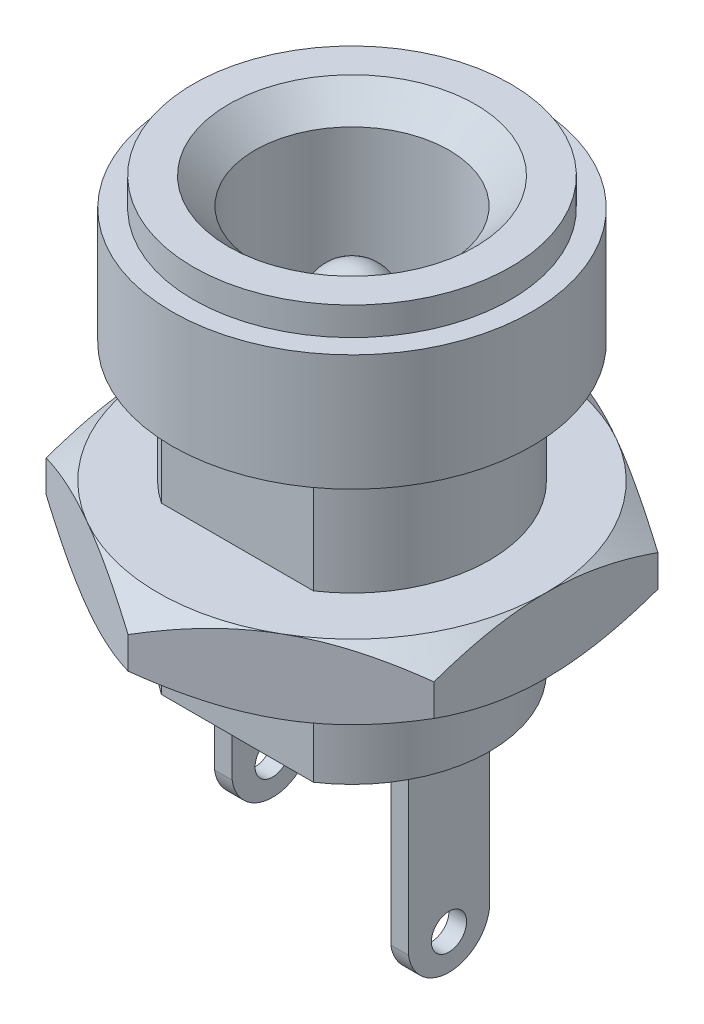
SolidWorks part; units mm, degrees
ref_plane "Front Plane" through (0, 0, 0) normal (0, 0, 1) x (1, 0, 0)
ref_plane "Top Plane" through (0, 0, 0) normal (0, 1, 0) x (1, 0, 0)
ref_plane "Right Plane" through (0, 0, 0) normal (1, 0, 0) x (0, 0, -1)
sketch "Sketch1" plane through (0, 0, 0) normal (0, 0, 1) x (1, 0, 0)
  line L0 (0, 0) -> (0, 12.2) construction
  line L1 (0, 0) -> (3.9, 0) construction
  line L2 (3.9, 0) -> (3.9, 8.1)
  line L3 (3.9, 8.1) -> (5.1, 8.1)
  line L4 (5.1, 8.1) -> (5.1, 11.4)
  line L5 (5.1, 11.4) -> (4.5, 11.4)
  line L6 (4.5, 11.4) -> (4.5, 12.2)
  line L7 (4.5, 12.2) -> (0, 12.2) construction
  line L8 (4.5, 12.2) -> (3.5, 12.2)
  line L9 (3.5, 12.2) -> (2.75, 11.45)
  line L10 (2.75, 11.45) -> (2.75, 3.2)
  line L11 (2.75, 3.2) -> (1.05, 3.2)
  line L12 (1.05, 3.2) -> (1.05, 8.95)
  line L13 (0, 2) -> (1.3, 2)
  line L14 (1.3, 2) -> (1.3, 0)
  line L15 (1.3, 0) -> (3.9, 0)
  line L16 (0, 10) -> (0, 2)
  arc A0 (1.05, 8.95) -> (0, 10) centre (0, 8.95) ccw
  dimension "D1" = 7.8
  dimension "D2" = 12.2
  dimension "D3" = 10.2
  dimension "D4" = 9
  dimension "D5" = 0.8
  dimension "D6" = 4.1
  dimension "D7" = 45
  dimension "D8" = 5.5
  dimension "D9" = 1
  dimension "D10" = 9
  dimension "D11" = 2.1
  dimension "D12" = 2.2
  dimension "D13" = 2.6
  dimension "D14" = 2
revolve "Revolve1" add sketch "Sketch1" angle 360 about L16
sketch "Sketch2" plane through (0, 0, 0) normal (0, -1, 0) x (1, 0, 0)
  line L0 (2.25, 0) -> (0, 0) construction
  line L1 (2.25, 1.15) -> (2.75, 1.15)
  line L2 (2.25, 1.15) -> (2.25, -1.15)
  line L3 (2.25, -1.15) -> (2.75, -1.15)
  line L4 (2.75, 1.15) -> (2.75, -1.15)
  line L5 (0, 0) -> (-2.25, 0) construction
  line L6 (-2.25, 1.15) -> (-2.75, 1.15)
  line L7 (-2.25, 1.15) -> (-2.25, -1.15)
  line L8 (-2.25, -1.15) -> (-2.75, -1.15)
  line L9 (-2.75, 1.15) -> (-2.75, -1.15)
  dimension "D1" = 2.75
  dimension "D2" = 2.3
  dimension "D3" = 0.5
extrude "Boss-Extrude1" add sketch "Sketch2" along normal blind 6
sketch "Sketch3" plane through (-2.75, 0, 0) normal (-1, 0, 0) x (0, 0, 1)
  line L0 (-1.15, -6) -> (-1.15, 0) construction
  line L1 (1.15, -6) -> (-1.15, -6)
  line L2 (1.15, -6) -> (1.15, -4.2)
  line L3 (1.15, -4.2) -> (-1.15, -4.2)
  line L4 (-1.15, -6) -> (-1.15, -4.2)
  dimension "D1" = 4.2
extrude "Cut-Extrude1" cut sketch "Sketch3" against normal up to next
sketch "Sketch4" plane through (-2.75, 0, 0) normal (-1, 0, 0) x (0, 0, 1)
  line L2 (1.15, -4.2) -> (-1.15, -4.2) construction
  line L3 (1.15, -4.2) -> (1.15, 0) construction
  line L4 (-1.15, -4.2) -> (-1.15, 0) construction
  line L5 (-1.15, -6) -> (-1.15, 0) construction
  line L6 (1.15, -6) -> (1.15, 0) construction
  line L7 (1.15, -6) -> (-1.15, -6) construction
  line L8 (-1.15, -3.2) -> (-1.15, -4.4)
  line L9 (-1.15, -4.4) -> (1.15, -4.4)
  line L10 (1.15, -4.4) -> (1.15, -3.2)
  circle A0 centre (0, -3.2) radius 0.5
  arc A1 (-1.15, -3.2) -> (1.15, -3.2) centre (0, -3.0388) ccw
  circle A2 centre (0, -5) radius 0.5 construction
  arc A3 (-1.15, -5) -> (1.15, -5) centre (0, -4.8387) ccw construction
  dimension "D1" = 1
  dimension "D2" = 3.2
  dimension "D3" = 5
  dimension "D4" = 1.2
extrude "Cut-Extrude2" cut sketch "Sketch4" against normal up to next
sketch "Sketch5" plane through (2.25, 0, 0) normal (-1, 0, 0) x (0, 0, 1)
  line L0 (-1.15, -5) -> (-1.15, -6.5)
  line L1 (-1.15, -6.5) -> (1.15, -6.5)
  line L2 (1.15, -6.5) -> (1.15, -5)
  circle A0 centre (0, -5) radius 0.5 construction
  arc A1 (-1.15, -5) -> (1.15, -5) centre (0, -4.8387) ccw construction
  circle A2 centre (0, -5) radius 0.5
  arc A3 (-1.15, -5) -> (1.15, -5) centre (0, -4.8387) ccw
  dimension "D1" = 1.5
extrude "Cut-Extrude3" cut sketch "Sketch5" against normal up to next
sketch "Sketch6" plane through (0, 0, 0) normal (0, -1, 0) x (1, 0, 0)
  line L0 (0, 3.25) -> (0, -3.25) construction
  line L1 (-5, 3.25) -> (5, 3.25)
  line L2 (-5, 3.25) -> (-5, 13.25)
  line L3 (-5, 13.25) -> (5, 13.25)
  line L4 (5, 3.25) -> (5, 13.25)
  line L5 (5, -3.25) -> (-5, -3.25)
  line L6 (5, -3.25) -> (5, -13.25)
  line L7 (5, -13.25) -> (-5, -13.25)
  line L8 (-5, -3.25) -> (-5, -13.25)
  point P10 (0, 0)
  dimension "D1" = 6.5
  dimension "D2" = 10
extrude "Cut-Extrude4" cut sketch "Sketch6" against normal up to surface (8.1 mm away) up to face at (0, 8.1, 5.1)
ref_plane "Plane1" through (0, 4.7, 0) normal (0, -1, 0) x (-1, 0, 0)
sketch "Sketch7" plane through (0, 4.7, 0) normal (0, -1, 0) x (-1, 0, 0)
  line L1 (0, 6.3509) -> (-5.5, 3.1754)
  line L2 (-5.5, 3.1754) -> (-5.5, -3.1754)
  line L3 (-5.5, -3.1754) -> (0, -6.3509)
  line L4 (0, -6.3509) -> (5.5, -3.1754)
  line L5 (5.5, -3.1754) -> (5.5, 3.1754)
  line L6 (5.5, 3.1754) -> (0, 6.3509)
  circle A0 centre (0, 0) radius 5.5 construction
  dimension "D1" = 11
extrude "Boss-Extrude2" add sketch "Sketch7" along normal blind 2.1
fillet "Fillet1" [suppressed] radius 0.5
sketch "Sketch9" plane through (0, 0, 0) normal (1, 0, 0) x (0, 0, -1)
  line L0 (6.3509, 4.1) -> (5.5, 4.7)
  line L1 (6.3509, 2.6) -> (6.3509, 4.7) construction
  line L2 (6.3509, 4.7) -> (3.1754, 4.7) construction
  line L3 (0, 0) -> (0, 4.7) construction
  line L4 (-3.25, 0) -> (3.25, 0) construction
  line L5 (3.1754, 4.7) -> (-3.1754, 4.7) construction
  line L6 (6.3509, 3.2) -> (5.5, 2.6)
  line L7 (6.3509, 2.6) -> (3.1754, 2.6) construction
  line L8 (6.3509, 4.1) -> (6.3509, 3.2) construction
  line L9 (6.3509, 3.65) -> (0, 3.65) construction
  line L10 (5.5, 4.7) -> (8.5, 4.7)
  line L11 (8.5, 4.7) -> (8.5, 2.6)
  line L12 (8.5, 2.6) -> (5.5, 2.6)
  line L13 (6.3509, 4.1) -> (6.3509, 3.2)
  dimension "D1" = 11
  dimension "D2" = 0.9
  dimension "D3" = 3
revolve "Cut-Revolve1" cut sketch "Sketch9" angle 360 about L3
